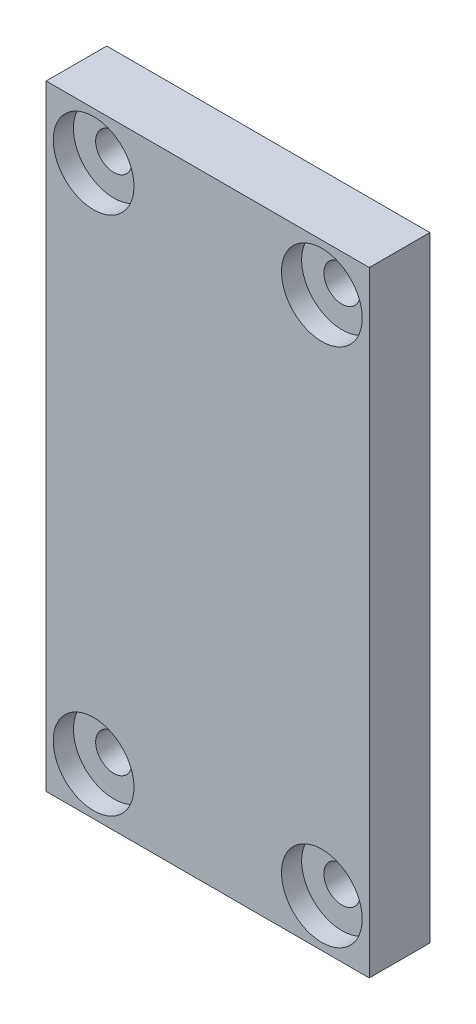
SolidWorks part; units mm, degrees
ref_plane "Front Plane" through (0, 0, 0) normal (0, 0, 1) x (1, 0, 0)
ref_plane "Top Plane" through (0, 0, 0) normal (0, 1, 0) x (1, 0, 0)
ref_plane "Right Plane" through (0, 0, 0) normal (1, 0, 0) x (0, 0, -1)
sketch "Sketch1" plane through (0, 0, 0) normal (0, 0, 1) x (1, 0, 0)
  line L1 (11.9174, 12.89) -> (23.2239, 12.89)
  line L2 (9.5674, 15.24) -> (25.5739, 15.24)
  line L3 (9.5674, 15.24) -> (9.5674, -15.24)
  line L4 (9.5674, -15.24) -> (25.5739, -15.24)
  line L5 (25.5739, 15.24) -> (25.5739, -15.24)
  line L6 (17.5707, -15.24) -> (17.5707, 15.24) construction
  line L7 (9.5674, 0) -> (25.5739, 0) construction
  line L8 (23.2239, 12.89) -> (23.2239, -12.89)
  line L9 (11.9174, -12.89) -> (23.2239, -12.89)
  line L10 (11.9174, 12.89) -> (11.9174, -12.89)
  circle A2 centre (11.9174, 12.89) radius 0.9
  circle A3 centre (23.2239, 12.89) radius 0.9
  circle A4 centre (23.2239, -12.89) radius 0.9
  circle A5 centre (11.9174, -12.89) radius 0.9
  point P230 (17.5707, 0)
  dimension "D1" = 2.35
  dimension "D2" = 1.8
extrude "Boss-Extrude1" add sketch "Sketch1" along normal blind 3 contours L5 L2 L3 L4 A5 L10 A2 L1 A3 L8 A4 L9 | A5 L9 A4 L8 A3 L1 A2 L10
sketch "Sketch2" plane through (0, 0, 3) normal (0, 0, 1) x (1, 0, 0)
  circle A4 centre (23.2239, 12.89) radius 2
  circle A5 centre (23.2239, -12.89) radius 2
  circle A6 centre (11.9174, -12.89) radius 2
  circle A7 centre (11.9174, 12.89) radius 2
  dimension "D1" = 4
extrude "Cut-Extrude1" cut sketch "Sketch2" against normal blind 1
